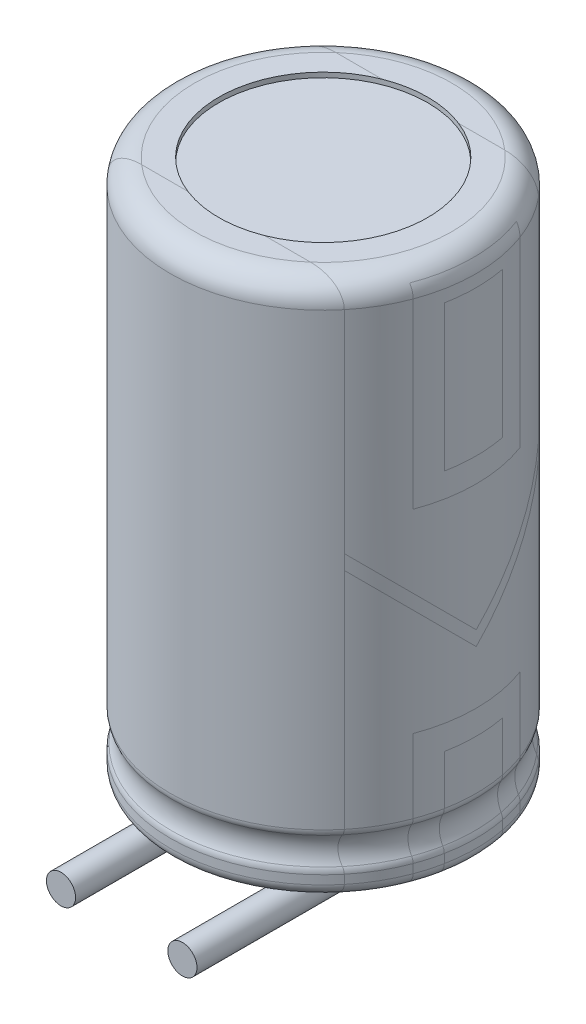
SolidWorks part; units mm, degrees
ref_plane "Front Plane" through (0, 0, 0) normal (0, 0, 1) x (1, 0, 0)
ref_plane "Top Plane" through (0, 0, 0) normal (0, 1, 0) x (1, 0, 0)
ref_plane "Right Plane" through (0, 0, 0) normal (1, 0, 0) x (0, 0, -1)
sketch "Sketch1" plane through (0, 0, 0) normal (0, 0, 1) x (1, 0, 0)
  line L0 (0, 0) -> (0, 58.059) construction
  line L1 (0, 10.9) -> (2.15, 10.9)
  line L2 (2.15, 10.9) -> (2.15, 11)
  line L3 (2.15, 11) -> (2.65, 11)
  line L4 (3.15, 10.5) -> (3.15, 1.2317)
  line L5 (0, 0) -> (2.9, 0)
  line L6 (3.15, 0.25) -> (3.15, 0.4317)
  line L7 (0, 0) -> (0, 10.9)
  arc A0 (3.1206, 0.5493) -> (3.1206, 1.114) centre (3.65, 0.8317) cw
  arc A1 (3.15, 1.2317) -> (3.1206, 1.114) centre (2.9, 1.2317) cw
  arc A2 (3.1206, 0.5493) -> (3.15, 0.4317) centre (2.9, 0.4317) cw
  arc A3 (2.9, 0) -> (3.15, 0.25) centre (2.9, 0.25) ccw
  arc A4 (3.15, 10.5) -> (2.65, 11) centre (2.65, 10.5) ccw
  point P15 (3.15, 0.5)
  point P18 (3.15, 0)
  dimension "D5" = 0.6
  dimension "D8" = 0.5
  dimension "D9" = 0.25
  dimension "D1" = 11
  dimension "D2" = 0.1
  dimension "D3" = 1
  dimension "D4" = 3.15
  dimension "D6" = 0.5
  dimension "D7" = 0.5
revolve "Revolve1" add sketch "Sketch1" angle 360 about L0
sketch "Sketch2" plane through (0, 0, 0) normal (1, 0, 0) x (0, 0, -1)
  line L0 (-2.9, 0) -> (2.9, 0) construction
  line L1 (-2, 11) -> (2, 11)
  line L2 (-2, 11) -> (-2, 0)
  line L3 (-2, 0) -> (2, 0)
  line L4 (2, 11) -> (2, 0)
  line L5 (2.15, 11) -> (-2.15, 11) construction
  dimension "D1" = 4
split line "Split Line1"
sketch "Sketch3" plane through (0, 0, 0) normal (1, 0, 0) x (0, 0, -1)
  line L0 (-1.1, 2.75) -> (1.1, 2.75)
  line L1 (-1.1, 10.75) -> (1.1, 10.75)
  line L2 (-1.1, 10.75) -> (-1.1, 6.75)
  line L3 (-1.1, 6.75) -> (1.1, 6.75)
  line L4 (1.1, 10.75) -> (1.1, 6.75)
  line L5 (-0.6, 10.25) -> (0.6, 10.25)
  line L6 (-0.6, 10.25) -> (-0.6, 7.25)
  line L7 (-0.6, 7.25) -> (0.6, 7.25)
  line L8 (0.6, 10.25) -> (0.6, 7.25)
  line L9 (-1.1, 2.75) -> (-1.1, -1.25)
  line L10 (-1.1, -1.25) -> (1.1, -1.25)
  line L11 (1.1, 2.75) -> (1.1, -1.25)
  line L12 (-0.6, 2.25) -> (0.6, 2.25)
  line L13 (-0.6, 2.25) -> (-0.6, -0.75)
  line L14 (-0.6, -0.75) -> (0.6, -0.75)
  line L15 (0.6, 2.25) -> (0.6, -0.75)
  line L16 (-1.1, -5.25) -> (1.1, -5.25)
  line L17 (-1.1, -5.25) -> (-1.1, -9.25)
  line L18 (-1.1, -9.25) -> (1.1, -9.25)
  line L19 (1.1, -5.25) -> (1.1, -9.25)
  line L20 (-0.6, -5.75) -> (0.6, -5.75)
  line L21 (-0.6, -5.75) -> (-0.6, -8.75)
  line L22 (-0.6, -8.75) -> (0.6, -8.75)
  line L23 (0.6, -5.75) -> (0.6, -8.75)
  line L24 (-1.1, -13.25) -> (1.1, -13.25)
  line L25 (-1.1, -13.25) -> (-1.1, -17.25)
  line L26 (-1.1, -17.25) -> (1.1, -17.25)
  line L27 (1.1, -13.25) -> (1.1, -17.25)
  line L28 (-0.6, -13.75) -> (0.6, -13.75)
  line L29 (-0.6, -13.75) -> (-0.6, -16.75)
  line L30 (-0.6, -16.75) -> (0.6, -16.75)
  line L31 (0.6, -13.75) -> (0.6, -16.75)
  line L32 (0, 0) -> (0, -17.25) construction
  line L33 (0, -17.25) -> (0, -16.75) construction
  line L34 (2.15, 11) -> (2, 11) construction
  line L35 (-2, 6.15) -> (-2, 5.85)
  line L36 (-2, 1.2317) -> (-2, 10.5) construction
  line L37 (-2, 5.85) -> (0, 3.85)
  line L38 (0, 3.85) -> (2, 5.85)
  line L39 (2, 10.5) -> (2, 1.2317) construction
  line L40 (2, 5.85) -> (2, 6.15)
  line L41 (2, 6.15) -> (0, 4.15)
  line L42 (0, 4.15) -> (-2, 6.15)
  line L43 (2, 6.15) -> (-2, 6.15) construction
  line L44 (0, 4.15) -> (0, 3.85) construction
  line L45 (0, 2.75) -> (0, 3.85) construction
  line L46 (2, -2.15) -> (2, -1.85)
  line L47 (2, -1.85) -> (0, -3.85)
  line L48 (0, -4.15) -> (2, -2.15)
  line L49 (-2, -2.15) -> (0, -4.15)
  line L50 (0, -3.85) -> (-2, -1.85)
  line L51 (-2, -1.85) -> (-2, -2.15)
  line L52 (2, -10.15) -> (2, -9.85)
  line L53 (2, -9.85) -> (0, -11.85)
  line L54 (0, -12.15) -> (2, -10.15)
  line L55 (-2, -10.15) -> (0, -12.15)
  line L56 (0, -11.85) -> (-2, -9.85)
  line L57 (-2, -9.85) -> (-2, -10.15)
  line L58 (2, -18.15) -> (2, -17.85)
  line L59 (2, -17.85) -> (0, -19.85)
  line L60 (0, -20.15) -> (2, -18.15)
  line L61 (-2, -18.15) -> (0, -20.15)
  line L62 (0, -19.85) -> (-2, -17.85)
  line L63 (-2, -17.85) -> (-2, -18.15)
  dimension "D1" = 4
  dimension "D2" = 3
  dimension "D3" = 2.2
  dimension "D4" = 1.2
  dimension "D5" = 0.5
  dimension "D6" = 0.5
  dimension "D7" = 0.5
  dimension "D8" = 0.5
  dimension "D9" = 0.25
  dimension "D10" = 4
  dimension "D11" = 4
  dimension "D12" = 4
  dimension "D13" = 0.3
  dimension "D14" = 0.3
  dimension "D15" = 90
  dimension "D16" = 2.6
  dimension "D17" = 4
  dimension "D18" = 1.1
split line "Split Line2"
sketch "Sketch4" plane through (0, 0, 0) normal (0, -1, 0) x (1, 0, 0)
  line L1 (0, 0) -> (-1.25, 0) construction
  circle A1 centre (-1.25, 0) radius 0.3
  dimension "D1" = 1.25
  dimension "D2" = 0.6
ref_plane "Plane1" through (-1.25, 0, 0) normal (1, 0, 0) x (0, 0, -1)
sketch "Sketch5" plane through (-1.25, 0, 0) normal (1, 0, 0) x (0, 0, -1)
  line L0 (0, 0) -> (0, -0.1)
  line L1 (0.5, -0.6) -> (4.15, -0.6) construction
  line L2 (3.15, 1.2317) -> (3.15, 10.5) construction
  line L3 (2, 0) -> (2.9, 0) construction
  line L4 (-0.5, -0.6) -> (-4.15, -0.6)
  arc A0 (0, -0.1) -> (0.5, -0.6) centre (0.5, -0.1) ccw construction
  arc A1 (-0.5, -0.6) -> (0, -0.1) centre (-0.5, -0.1) ccw
  dimension "D1" = 0.5
  dimension "D2" = 1
  dimension "D3" = 0.6
sweep "Sweep1" add profiles "Sketch4" path "Sketch5"
mirror "Mirror1" about plane through (0, 0, 0) normal (1, 0, 0) of "Sweep1"
